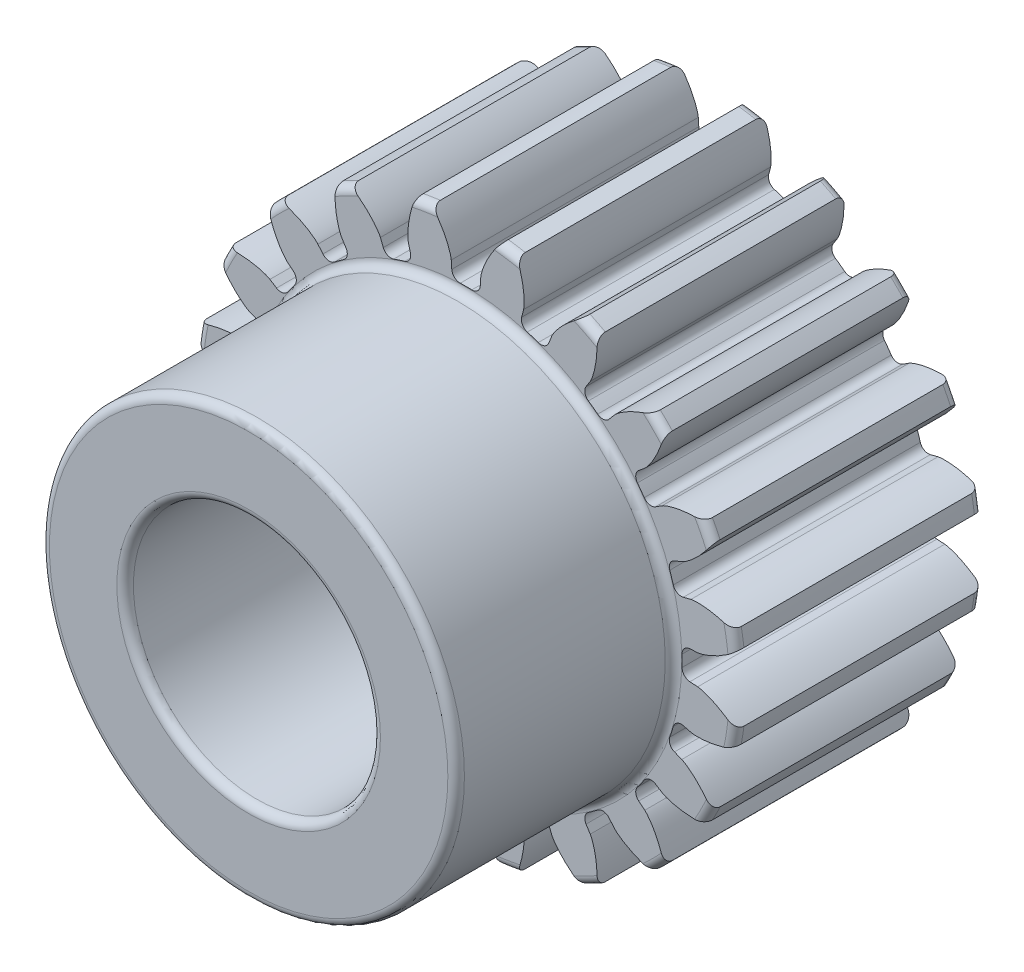
SolidWorks part; units mm, degrees
ref_plane "Front Plane" through (0, 0, 0) normal (0, 0, 1) x (1, 0, 0)
ref_plane "Top Plane" through (0, 0, 0) normal (0, 1, 0) x (1, 0, 0)
ref_plane "Right Plane" through (0, 0, 0) normal (1, 0, 0) x (0, 0, -1)
sketch "Sketch1" plane through (0, 0, 0) normal (0, 0, 1) x (1, 0, 0)
  line L0 (0, 0) -> (0, 12.7) construction
  line L1 (-4.0817, 14.1856) -> (4.0817, 11.2144) construction
  circle A0 centre (0, 0) radius 11.1125 construction
  circle A1 centre (0, 0) radius 13.97 construction
  circle A2 centre (0, 0) radius 12.7 construction
  circle A3 centre (0, 0) radius 11.9341 construction
  circle A4 centre (0, 0) radius 6.35 construction
  circle A5 centre (0, 0) radius 10.668 construction
  point P8 (254, 0)
  point P13 (254, 0)
  dimension "OD | Outside Diameter" = 27.94
  dimension "Root Diameter" = 22.225
  dimension "Gear Pitch Diameter" = 25.4
  dimension "Base Diameter" = 23.8682
  dimension "For Shaft Diameter" = 12.7
  dimension "Hub Diameter" = 21.336
  dimension "Pressure Angle" = 20
  dimension "Number of Teeth" = 508
  dimension "Gear Pitch | Diametral Pitch" = 508
sketch "Sketch2" plane through (0, 0, 0) normal (1, 0, 0) x (0, 0, -1)
  line L0 (-11.938, 0) -> (11.938, 0) construction
  line L1 (-11.938, 13.97) -> (11.938, 13.97) construction
  point P2 (0, 13.97)
  point P4 (-0.762, 0)
  point P6 (-0.762, 13.97)
  dimension "Overall Width" = 23.876
  dimension "Hub Width" = 11.176
  dimension "Face Width" = 12.7
sketch "Sketch3" plane through (0, 0, 0) normal (0, 0, 1) x (1, 0, 0)
  circle A0 centre (0, 0) radius 13.97
  circle A1 centre (0, 0) radius 13.97 construction
extrude "Boss-Extrude1" add sketch "Sketch3" against normal up to vertex (11.938 mm away) and the other way up to vertex (11.938 mm away) up to point (0, 0, -11.938) other way up to point (0, 0, 11.938)
sketch "Sketch5" plane through (0, 0, 0) normal (1, 0, 0) x (0, 0, -1)
  line L1 (-11.938, 13.97) -> (-0.762, 13.97)
  line L2 (-11.938, 13.97) -> (-11.938, 10.668)
  line L3 (-11.938, 10.668) -> (-0.762, 10.668)
  line L4 (-0.762, 13.97) -> (-0.762, 10.668)
  line L11 (11.938, 6.35) -> (-11.938, 6.35)
  line L12 (11.938, 6.35) -> (11.938, 0)
  line L13 (11.938, 0) -> (-11.938, 0)
  line L14 (-11.938, 6.35) -> (-11.938, 0)
  point P5 (0, 6.35)
  point P12 (0, 10.668)
revolve "Cut-Revolve1" cut sketch "Sketch5" angle 360 about L0
fillet "Fillet2" radius 0.4261 6 edges at (13.97, 0, -11.938) (6.35, 0, -11.938) (6.35, 0, 11.938) (10.668, 0, 0.762) (13.97, 0, 0.762) (10.668, 0, 11.938)
sketch "Sketch4" plane through (0, 0, 0) normal (0, 0, 1) x (1, 0, 0)
  line L0 (0, 0) -> (11.09, 0.7067) construction
  line L2 (0, 0) -> (11.09, -0.7067) construction
  line L4 (11.09, 0.7067) -> (11.9099, 0.7589)
  line L5 (11.9099, -0.7589) -> (11.09, -0.7067)
  arc A0 (11.09, 0.7067) -> (11.09, -0.7067) centre (0, 0) cw
  arc A3 (13.8601, 1.7486) -> (13.8601, -1.7486) centre (0, 0) cw
  circle A4 centre (0, 0) radius 13.97 construction
  spline S0 degree 4 poles (11.9099, 0.7589) (11.9132, 0.7592) (11.9223, 0.76) (11.9395, 0.7621) (11.9676, 0.7662) (12.0032, 0.7725) (12.049, 0.7819) (12.1028, 0.7946) (12.1617, 0.8101) (12.2255, 0.8288) (12.2889, 0.849) (12.3518, 0.8706) (12.4142, 0.8934) (12.4896, 0.9225) (12.5794, 0.9596) (12.6838, 1.0061) (12.8012, 1.0624) (12.9199, 1.1237) (13.0359, 1.1872) (13.152, 1.255) (13.2636, 1.3231) (13.3784, 1.3975) (13.4837, 1.4681) (13.6005, 1.5512) (13.6943, 1.6195) (13.8166, 1.7137) (13.8883, 1.7707) (13.9718, 1.8388) (14.0086, 1.8698) (14.0312, 1.8889) knots 0 0 0 0 0 0.005377 0.015084 0.028532 0.04661 0.064855 0.092111 0.119476 0.146842 0.174209 0.201575 0.228941 0.256307 0.307035 0.361767 0.4165 0.471232 0.525964 0.580697 0.635429 0.690161 0.744894 0.799626 0.854358 0.909091 0.954545 1 1 1 1 1 construction
  spline S1 degree 4 poles (11.9099, 0.7589) (11.9132, 0.7592) (11.9223, 0.76) (11.9395, 0.7621) (11.9676, 0.7662) (12.0032, 0.7725) (12.049, 0.7819) (12.1028, 0.7946) (12.1617, 0.8101) (12.2255, 0.8288) (12.2889, 0.849) (12.3518, 0.8706) (12.4142, 0.8934) (12.4896, 0.9225) (12.5794, 0.9596) (12.6838, 1.0061) (12.8012, 1.0624) (12.9199, 1.1237) (13.0359, 1.1872) (13.152, 1.255) (13.2636, 1.3231) (13.3784, 1.3975) (13.4837, 1.4681) (13.6005, 1.5512) (13.6943, 1.6195) (13.79, 1.6933) (13.8365, 1.7297) (13.8601, 1.7486) knots 0 0 0 0 0 0.005377 0.015084 0.028532 0.04661 0.064855 0.092111 0.119476 0.146842 0.174209 0.201575 0.228941 0.256307 0.307035 0.361767 0.4165 0.471232 0.525964 0.580697 0.635429 0.690161 0.744894 0.799626 0.854358 0.909091 0.909091 0.909091 0.909091 0.909091
  spline S2 degree 4 poles (11.9099, -0.7589) (11.9132, -0.7592) (11.9223, -0.76) (11.9395, -0.7621) (11.9676, -0.7662) (12.0032, -0.7725) (12.049, -0.7819) (12.1028, -0.7946) (12.1617, -0.8101) (12.2255, -0.8288) (12.2889, -0.849) (12.3518, -0.8706) (12.4142, -0.8934) (12.4896, -0.9225) (12.5794, -0.9596) (12.6838, -1.0061) (12.8012, -1.0624) (12.9199, -1.1237) (13.0359, -1.1872) (13.152, -1.255) (13.2636, -1.3231) (13.3784, -1.3975) (13.4837, -1.4681) (13.6005, -1.5512) (13.6943, -1.6195) (13.8166, -1.7137) (13.8883, -1.7707) (13.9718, -1.8388) (14.0086, -1.8698) (14.0312, -1.8889) knots 0 0 0 0 0 0.005377 0.015084 0.028532 0.04661 0.064855 0.092111 0.119476 0.146842 0.174209 0.201575 0.228941 0.256307 0.307035 0.361767 0.4165 0.471232 0.525964 0.580697 0.635429 0.690161 0.744894 0.799626 0.854358 0.909091 0.954545 1 1 1 1 1 construction
  spline S3 degree 4 poles (11.9099, -0.7589) (11.9132, -0.7592) (11.9223, -0.76) (11.9395, -0.7621) (11.9676, -0.7662) (12.0032, -0.7725) (12.049, -0.7819) (12.1028, -0.7946) (12.1617, -0.8101) (12.2255, -0.8288) (12.2889, -0.849) (12.3518, -0.8706) (12.4142, -0.8934) (12.4896, -0.9225) (12.5794, -0.9596) (12.6838, -1.0061) (12.8012, -1.0624) (12.9199, -1.1237) (13.0359, -1.1872) (13.152, -1.255) (13.2636, -1.3231) (13.3784, -1.3975) (13.4837, -1.4681) (13.6005, -1.5512) (13.6943, -1.6195) (13.79, -1.6933) (13.8365, -1.7297) (13.8601, -1.7486) knots 0 0 0 0 0 0.005377 0.015084 0.028532 0.04661 0.064855 0.092111 0.119476 0.146842 0.174209 0.201575 0.228941 0.256307 0.307035 0.361767 0.4165 0.471232 0.525964 0.580697 0.635429 0.690161 0.744894 0.799626 0.854358 0.909091 0.909091 0.909091 0.909091 0.909091
  dimension "D1" = 22.225
extrude "Cut-Extrude1" cut sketch "Sketch4" against normal through all both and the other way through all
fillet "Fillet1" radius 0.4261 2 edges at (11.09, -0.7067, -5.588) (11.09, 0.7067, -5.588)
pattern_circular "CirPattern1" count 20 over 360 about axis through (0, 0, 11.938) along (0, 0, -1) of "Cut-Extrude1", "Fillet1"
equation "\"Root Diameter@Sketch1\"=\"Root Diameter\""
equation "\"OD | Outside Diameter@Sketch1\"=\"Outside Diameter\""
equation "\"D1@CirPattern1\"=\"Number of Teeth\""
equation "\"Diametral Pitch\"=20"
equation "\"Number of Teeth\"= 20"
equation "\"Pressure Angle\"=20"
equation "\"Pitch Diameter\"= \"Number of Teeth\" / \"Diametral Pitch\""
equation "\"Base Diameter\"= \"Pitch Diameter\" * cos ( \"Pressure Angle\" )"
equation "\"Outside Diameter\"= ( \"Number of Teeth\" + 2 ) / \"Diametral Pitch\""
equation "\"Dedendum\"= 1.25 / \"Diametral Pitch\""
equation "\"Root Diameter\"= \"Pitch Diameter\" - ( 2 * \"Dedendum\" )"
equation "\"Pitch Angle\"= 360deg / \"Number of Teeth\""
equation "\"Alpha\"= sqr ( \"Pitch Diameter\" ^ 2 - \"Base Diameter\" ^ 2 ) / \"Base Diameter\" * 180 / PI - \"Pressure Angle\""
equation "\"Beta\"= ( \"Pitch Angle\" / 4 - \"Alpha\" )"
equation "\"Phi\"= sqr ( ( \"Outside Diameter\" / 2 ) ^ 2 - ( \"Base Diameter\" / 2 ) ^ 2 ) / ( \"Base Diameter\" / 2 )"
equation "\"Addendum\"= 1 / \"Diametral Pitch\""
equation "\"WorkingDepth\"= 2 / \"Diametral Pitch\""
equation "\"WholeDepth\"= 2.25 / \"Diametral Pitch\""
equation "\"Clearance\"= 0.25 / \"Diametral Pitch\""
equation "\"ToothThickness\"= ( pi * 2 ) / \"Diametral Pitch\""
equation "\"CircularPitch\"= pi / \"Diametral Pitch\""
equation "\"Number of Teeth@Sketch1\"=\"Number of Teeth\""
equation "\"Gear Pitch | Diametral Pitch@Sketch1\"=\"Diametral Pitch\""
equation "\"Pressure Angle@Sketch1\"=\"Pressure Angle\""
equation "\"Gear Pitch Diameter@Sketch1\"=\"Pitch Diameter\""
equation "\"Base Diameter@Sketch1\"=\"Base Diameter\""
equation "\"Fillet\"= \"Clearance\" * cos ( \"Pressure Angle\" ) * tan ( ( 90 + \"Pressure Angle\" ) / 2 )"
equation "\"D1@Fillet1\"=\"Fillet\""
equation "\"D1@Sketch4\"=if( \"Base Diameter\">\"Root Diameter\",\"Root Diameter\",\"Base Diameter\"-.00001)"
equation "\"D1@Fillet2\"=\"Fillet\""
